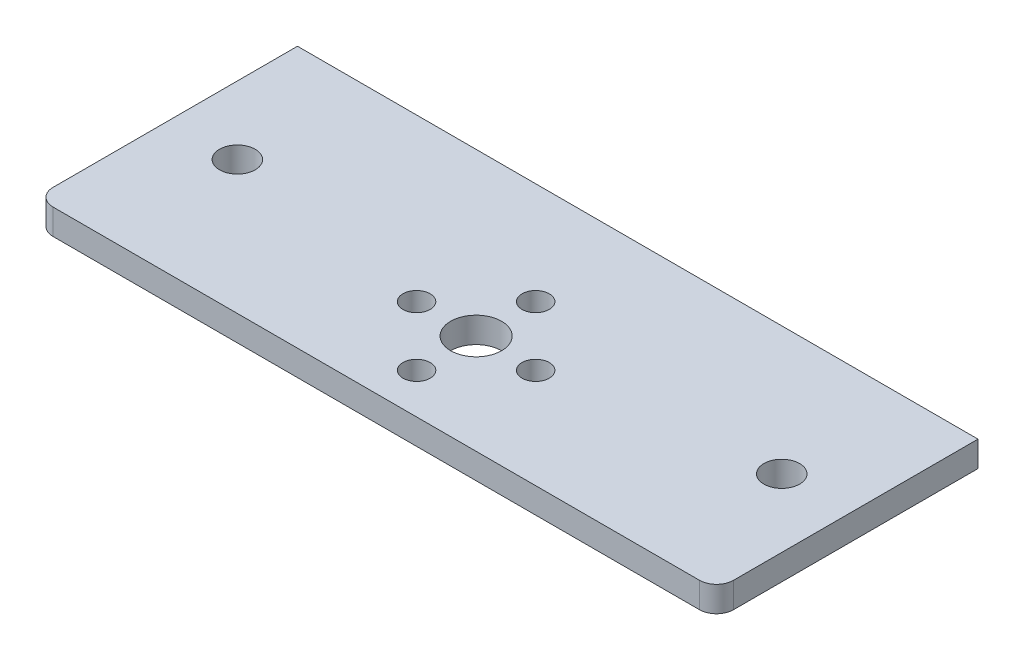
SolidWorks part; units mm, degrees
material "ABS PC"
ref_plane "Front Plane" through (0, 0, 0) normal (0, 0, 1) x (1, 0, 0)
ref_plane "Top Plane" through (0, 0, 0) normal (0, 1, 0) x (1, 0, 0)
ref_plane "Right Plane" through (0, 0, 0) normal (1, 0, 0) x (0, 0, -1)
sketch "Sketch1" plane through (0, 0, 0) normal (0, 1, 0) x (1, 0, 0)
  line L0 (0, 10.0592) -> (0, -12.4573) construction
  line L1 (-40, 19) -> (40, 19)
  line L2 (-40, 19) -> (-40, -11.74)
  line L3 (-40, -11.74) -> (40, -11.74)
  line L4 (40, 19) -> (40, -11.74)
  line L5 (-24.8375, 0) -> (25.6297, 0) construction
  circle A0 centre (0, 0) radius 3
  circle A1 centre (0, 7) radius 1.6
  circle A2 centre (-7, 0) radius 1.6
  circle A3 centre (0, -7) radius 1.6
  circle A4 centre (7, 0) radius 1.6
  circle A5 centre (0, 0) radius 7 construction
  dimension "D1" = 6
  dimension "D2" = 3.2
  dimension "D5" = 14
  dimension "D3" = 11.74
  dimension "D4" = 19
  dimension "D6" = 80
extrude "Boss-Extrude1" add sketch "Sketch1" against normal blind 3
sketch "Sketch2" plane through (0, 0, 0) normal (0, 1, 0) x (1, 0, 0)
  line L0 (-37.6115, 3.93) -> (35.7921, 3.93) construction
  line L1 (-31.999, 7.1081) -> (-31.999, -6.0471) construction
  line L2 (31.999, 7.1081) -> (31.999, -5.3474) construction
  line L3 (40, -11.74) -> (40, 19) construction
  line L4 (40, 19) -> (-40, 19) construction
  line L5 (-40, 19) -> (-40, -11.74) construction
  line L6 (40, -11.74) -> (40, 19) construction
  line L7 (40, 19) -> (-40, 19) construction
  line L8 (-40, 19) -> (-40, -11.74) construction
  circle A0 centre (31.999, 3.93) radius 2.1
  circle A1 centre (-31.999, 3.93) radius 2.1
  dimension "D1" = 15.07
  dimension "D2" = 4.2
  dimension "D3" = 8.001
  dimension "D4" = 8.001
extrude "Cut-Extrude1" cut sketch "Sketch2" against normal blind 10
fillet "Fillet1" radius 2 2 edges at (-40, -1.5, 11.74) (40, -1.5, 11.74)
